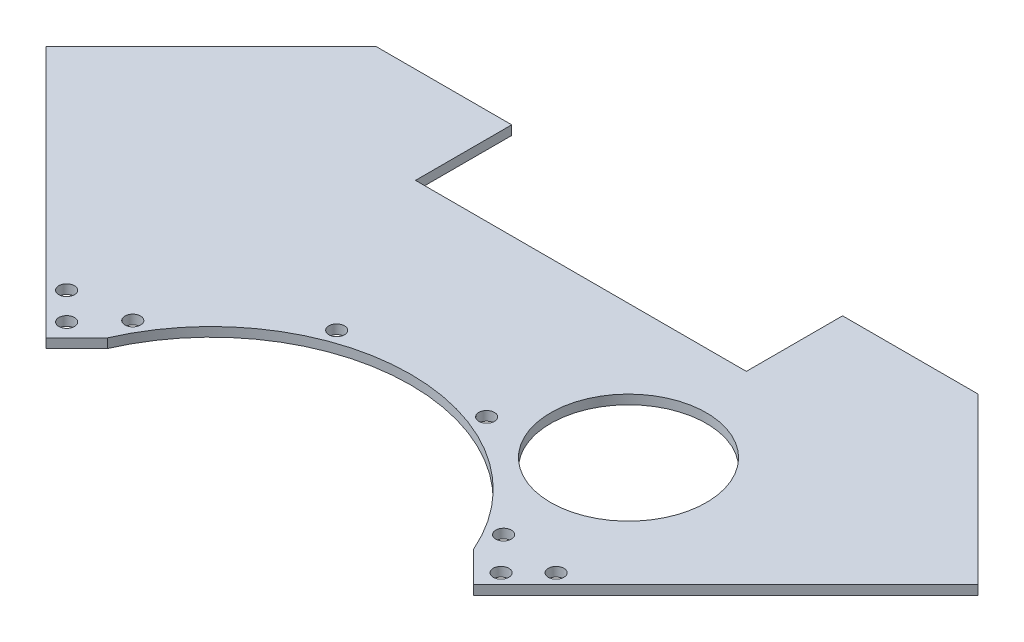
SolidWorks part; units mm, degrees
material "AISI Type A2 Tool Steel"
ref_plane "Front Plane" through (0, 0, 0) normal (0, 0, 1) x (1, 0, 0)
ref_plane "Top Plane" through (0, 0, 0) normal (0, 1, 0) x (1, 0, 0)
ref_plane "Right Plane" through (0, 0, 0) normal (1, 0, 0) x (0, 0, -1)
other "Bounding Box"
ref_plane "Default Plane" through (-8.9266, -12.7485, 0) normal (-0.1736, 0.9848, 0) x (0.9848, 0.1736, 0)
sketch "Sketch1" plane through (0, 0, 0) normal (0, 1, 0) x (1, 0, 0)
  line L0 (-78.7235, 24.8419) -> (78.7235, 24.8419) construction
  line L1 (0, 0) -> (139.7, 139.7) construction
  line L2 (0, 0) -> (-139.7, 139.7) construction
  line L3 (0, 0) -> (0, 165.1) construction
  line L4 (-139.7, 139.7) -> (139.7, 139.7) construction
  line L5 (-44.45, 203.2) -> (44.45, 203.2)
  line L6 (-44.45, 203.2) -> (-44.45, 127)
  line L7 (-44.45, 127) -> (44.45, 127)
  line L8 (44.45, 203.2) -> (44.45, 127)
  line L9 (-44.45, 203.2) -> (44.45, 127) construction
  line L10 (-44.45, 127) -> (44.45, 203.2) construction
  line L11 (-167.7633, 131.8423) -> (-131.8423, 167.7633)
  line L12 (-167.7633, 131.8423) -> (-147.5577, 111.6367)
  line L13 (-131.8423, 167.7633) -> (-111.6367, 147.5577)
  line L14 (-147.5577, 111.6367) -> (-111.6367, 147.5577)
  line L15 (-167.7633, 131.8423) -> (-111.6367, 147.5577) construction
  line L16 (-131.8423, 167.7633) -> (-147.5577, 111.6367) construction
  line L17 (131.8423, 167.7633) -> (167.7633, 131.8423)
  line L18 (131.8423, 167.7633) -> (111.6367, 147.5577)
  line L19 (167.7633, 131.8423) -> (147.5577, 111.6367)
  line L20 (111.6367, 147.5577) -> (147.5577, 111.6367)
  line L21 (131.8423, 167.7633) -> (147.5577, 111.6367) construction
  line L22 (167.7633, 131.8423) -> (111.6367, 147.5577) construction
  line L23 (-29.5981, 56.1801) -> (48.4616, 97.3054)
  line L24 (-9.525, -44.45) -> (9.525, -44.45)
  line L25 (-9.525, -44.45) -> (-9.525, 44.45)
  line L26 (-9.525, 44.45) -> (9.525, 44.45)
  line L27 (9.525, -44.45) -> (9.525, 44.45)
  line L28 (-9.525, -44.45) -> (9.525, 44.45) construction
  line L29 (-9.525, 44.45) -> (9.525, -44.45) construction
  line L30 (61.9263, -14.0491) -> (81.447, 71.9948)
  line L31 (78.7235, 24.8419) -> (194.7041, 140.8225)
  line L32 (-78.7235, 24.8419) -> (-194.7041, 140.8225)
  line L33 (-194.7041, 140.8225) -> (-138.6766, 196.85)
  line L34 (-138.6766, 196.85) -> (-53.975, 196.85)
  line L35 (-53.975, 196.85) -> (-53.975, 120.65)
  line L36 (-53.975, 120.65) -> (53.975, 120.65)
  line L37 (53.975, 120.65) -> (53.975, 196.85)
  line L38 (53.975, 196.85) -> (138.6766, 196.85)
  line L39 (138.6766, 196.85) -> (194.7041, 140.8225)
  line L40 (0, 0) -> (59.1288, 77.0581) construction
  circle A0 centre (0, 0) radius 63.5
  circle A1 centre (59.1288, 77.0581) radius 22.8854
  arc A2 (-78.7235, 24.8419) -> (78.7235, 24.8419) centre (0, 0) ccw
  circle A3 centre (59.1288, 77.0581) radius 29.5021
  point P4 (0, -82.55)
  point P39 (121.7395, 157.6605)
  point P44 (0, 63.5)
  dimension "D1" = 127
  dimension "D9" = 45.7708
  dimension "D12" = 19.05
  dimension "D20" = 59.0042
  dimension "D2" = 45
  dimension "D3" = 50.8
  dimension "D4" = 28.575
  dimension "D5" = 88.9
  dimension "D6" = 19.05
  dimension "D7" = 76.2
  dimension "D8" = 88.9
  dimension "D10" = 25.4
  dimension "D11" = 139.7
  dimension "D13" = 9.525
  dimension "D14" = 6.35
  dimension "D15" = 38.1
  dimension "D16" = 31.75
  dimension "D17" = 25.4
  dimension "D18" = 97.1296
  dimension "D19" = 37.5
sketch "Sketch2" plane through (0, 0, 0) normal (1, 0, 0) x (0, 0, -1)
  line L0 (-82.55, -25.4) -> (-82.55, 25.4)
  line L1 (-63.5, 17.78) -> (63.5, 17.78)
  line L2 (-63.5, 17.78) -> (-63.5, -17.78)
  line L3 (-63.5, -17.78) -> (63.5, -17.78)
  line L4 (63.5, 17.78) -> (63.5, -17.78)
  line L5 (-63.5, 17.78) -> (63.5, -17.78) construction
  line L6 (-63.5, -17.78) -> (63.5, 17.78) construction
  line L7 (-82.55, 25.4) -> (82.55, 25.4)
  line L8 (-82.55, -25.4) -> (63.5, -25.4)
  line L9 (63.5, -25.4) -> (63.5, -38.1)
  line L10 (0, -44.45) -> (25.3029, -44.45) construction
  line L11 (139.7, -44.45) -> (139.7, 6.35) construction
  line L12 (63.5, -38.1) -> (194.5388, -38.1)
  line L13 (165.1, 0) -> (165.1, -3.81) construction
  line L14 (203.2, -3.81) -> (203.2, 0) construction
  line L15 (165.1, -41.91) -> (165.1, -44.45) construction
  line L16 (157.6605, -19.05) -> (157.6605, 0) construction
  line L17 (196.85, -44.45) -> (181.8826, -3.3274)
  line L18 (181.8826, -3.3274) -> (82.55, -3.3274)
  line L19 (82.55, -3.3274) -> (82.55, 25.4)
  line L20 (63.5, -38.1) -> (63.5, -41.1226)
  line L21 (63.5, -41.1226) -> (195.6389, -41.1226)
  line L22 (82.55, -3.3274) -> (82.55, -6.35)
  line L23 (82.55, -6.35) -> (182.9827, -6.35)
  circle A0 centre (0, 0) radius 44.45
  circle A1 centre (165.1, -3.81) radius 38.1
  circle A2 centre (165.1, -3.81) radius 6.35
  ellipse E0 centre (139.7, -19.05) end of major axis (139.7, 6.35) minor radius 17.9605
  dimension "D4" = 12.7
  dimension "D1" = 35.56
  dimension "D2" = 50.8
  dimension "D3" = 50.8
  dimension "D5" = 34.29
  dimension "D6" = 12.7
  dimension "D7" = 70
  dimension "D8" = 3.0226
  dimension "D9" = 31.75
  dimension "D10" = 19.05
ref_plane "Plane1" through (-129.5972, 0, -129.5972) normal (-0.7071, 0, -0.7071) x (0.7071, 0, -0.7071)
sketch "Sketch5" plane through (-129.5972, 0, -129.5972) normal (-0.7071, 0, -0.7071) x (0.7071, 0, -0.7071)
  line L0 (-141421.3562, 44.45) -> (141439.2481, 44.45) construction
  line L1 (0, 19.05) -> (0, 0) construction
  circle A0 centre (0, 19.05) radius 25.4
  dimension "D1" = 50.8
sketch "Sketch3" plane through (0, 0, 0) normal (0, 1, 0) x (1, 0, 0)
  line L0 (64.2555, 10.3739) -> (152.0479, 98.1663)
  line L1 (78.7235, 24.8419) -> (194.7041, 140.8225) construction
  line L2 (152.0479, 98.1663) -> (98.1663, 152.0479)
  line L3 (98.1663, 152.0479) -> (53.975, 152.0479)
  line L4 (53.975, 120.65) -> (53.975, 196.85) construction
  line L5 (53.975, 152.0479) -> (53.975, 120.65)
  line L6 (53.975, 120.65) -> (-53.975, 120.65)
  line L7 (-53.975, 120.65) -> (-53.975, 152.0479)
  line L8 (-53.975, 196.85) -> (-53.975, 120.65) construction
  line L9 (-53.975, 152.0479) -> (-98.1663, 152.0479)
  line L10 (-98.1663, 152.0479) -> (-152.0479, 98.1663)
  line L11 (-78.7235, 24.8419) -> (-194.7041, 140.8225) construction
  line L12 (-152.0479, 98.1663) -> (-64.2555, 10.3739)
  line L13 (-147.5577, 111.6367) -> (-111.6367, 147.5577) construction
  line L14 (111.6367, 147.5577) -> (147.5577, 111.6367) construction
  line L15 (0, 0) -> (-139.7, 139.7) construction
  arc A0 (-64.2555, 10.3739) -> (64.2555, 10.3739) centre (0, 0) cw
  circle A2 centre (0, 0) radius 63.5 construction
  point P34 (-125.1071, 125.1071)
  dimension "D1" = 1.5875
  dimension "D2" = 6.35
extrude "Boss-Extrude1" add sketch "Sketch3" along normal mid plane 3.0226
sketch "Sketch4" plane through (0, 1.5113, 0) normal (0, 1, 0) x (1, 0, 0)
  line L1 (0, 0) -> (24.462, 65.4266) construction
  line L2 (0, 0) -> (60.4919, 34.925) construction
  line L3 (0, 0) -> (23.1311, 0) construction
  line L4 (0, 0) -> (0, 21.8416) construction
  circle A0 centre (24.462, 65.4266) radius 2.5527
  circle A1 centre (24.462, 65.4266) radius 4.7625 construction
  arc A2 (64.2555, 10.3739) -> (-64.2555, 10.3739) centre (0, 0) ccw construction
  circle A3 centre (60.4919, 34.925) radius 2.5527
  circle A4 centre (60.4919, 34.925) radius 4.7625 construction
  circle A5 centre (-60.4919, 34.925) radius 2.5527
  circle A6 centre (-24.462, 65.4266) radius 2.5527
  dimension "D1" = 5.1054
  dimension "D2" = 9.525
  dimension "D3" = 20.5
  dimension "D4" = 30
extrude "Cut-Extrude1" cut sketch "Sketch4" against normal through all
sketch "Sketch6" plane through (0, 1.5113, 0) normal (0, 1, 0) x (1, 0, 0)
  line L0 (78.7235, 24.8419) -> (69.7432, 15.8617) construction
  line L1 (64.2555, 10.3739) -> (152.0479, 98.1663) construction
  line L2 (69.7432, 15.8617) -> (60.7629, 24.8419)
  line L3 (60.7629, 24.8419) -> (73.5003, 37.5793) construction
  line L4 (78.7235, 24.8419) -> (73.5003, 37.5793) construction
  line L5 (60.7629, 24.8419) -> (59.7182, 25.8866)
  line L6 (59.7182, 25.8866) -> (64.2555, 10.3739)
  line L7 (64.2555, 10.3739) -> (69.7432, 15.8617)
  circle A0 centre (0, 0) radius 82.55 construction
  arc A1 (64.2555, 10.3739) -> (-64.2555, 10.3739) centre (0, 0) ccw construction
  dimension "D1" = 165.1
  dimension "D2" = 12.7
  dimension "D3" = 12.7
extrude "Cut-Extrude4" cut sketch "Sketch6" against normal through all
sketch "Sketch7" plane through (0, 1.5113, 0) normal (0, 1, 0) x (1, 0, 0)
  line L0 (66.3756, 19.2293) -> (70.8657, 23.7194) construction
  line L2 (70.8657, 23.7194) -> (79.846, 32.6996) construction
  line L3 (69.7432, 15.8617) -> (59.7182, 25.8866) construction
  line L4 (78.7235, 24.8419) -> (194.7041, 140.8225) construction
  circle A0 centre (70.8657, 23.7194) radius 2.5527
  circle A1 centre (79.846, 32.6996) radius 2.5527
  dimension "D1" = 5.1054
  dimension "D2" = 6.35
  dimension "D3" = 12.7
  dimension "D4" = 4.7625
extrude "Cut-Extrude2" cut sketch "Sketch7" against normal through all
sketch "Sketch22" [suppressed] plane through (0, 1.5113, 0) normal (0, 1, 0) x (1, 0, 0)
  circle A0 centre (59.1288, 77.0581) radius 31.75
  dimension "D1" = 63.5
extrude "Cut-Extrude5" [suppressed] cut sketch "Sketch22" against normal through all
mirror "Mirror1" about plane through (0, 0, 0) normal (1, 0, 0) of "Cut-Extrude4", "Cut-Extrude2"
sketch "Sketch8" plane through (0, 1.5113, 0) normal (0, 1, 0) x (1, 0, 0)
  circle A0 centre (59.1288, 77.0581) radius 25.4
  dimension "D1" = 50.8
extrude "Cut-Extrude3" cut sketch "Sketch8" against normal through all
ref_plane "Plane2" [suppressed] through (26.9408, 0, 26.9408) normal (-0.7071, 0, -0.7071) x (0.7071, 0, -0.7071)
sketch "Sketch10" [suppressed] plane through (26.9408, 0, 26.9408) normal (-0.7071, 0, -0.7071) x (0.7071, 0, -0.7071)
  line L0 (-141421.3562, 44.45) -> (141439.2481, 44.45) construction
  line L1 (-141421.3562, 44.45) -> (141439.2481, 44.45) construction
  line L2 (44.9013, 41.1226) -> (237.2531, 41.1226)
  line L3 (237.2531, 41.1226) -> (223.4968, 3.3274)
  line L4 (223.4968, 3.3274) -> (58.3717, 3.3274)
  line L5 (237.2531, 41.1226) -> (238.4642, 44.45)
  dimension "D1" = 70
ref_plane "Plane5" [suppressed] through (0, -44.45, 0) normal (0, 1, 0) x (1, 0, 0)
ref_plane "Plane6" [suppressed] through (0, -3.3274, 0) normal (0, 1, 0) x (1, 0, 0)
sketch "Sketch20" [suppressed] plane through (0, -3.3274, 0) normal (0, 1, 0) x (1, 0, 0)
  line L0 (184.9769, 131.0953) -> (134.1896, 181.8826)
  line L1 (134.1896, 181.8826) -> (53.975, 181.8826)
  line L2 (138.6766, 196.85) -> (194.7041, 140.8225) construction
  line L3 (53.975, 120.65) -> (53.975, 196.85) construction
  line L4 (184.9769, 131.0953) -> (186.5933, 132.7118) construction
  line L5 (186.5933, 132.7118) -> (135.1365, 184.1686)
  line L6 (135.1365, 184.1686) -> (53.975, 184.1686)
  line L7 (53.975, 184.1686) -> (53.975, 181.8826)
  line L8 (184.9769, 131.0953) -> (187.1142, 128.958)
  line L9 (187.1142, 128.958) -> (188.7306, 130.5745)
  line L10 (188.7306, 130.5745) -> (186.5933, 132.7118)
  dimension "D1" = 2.286
  dimension "D2" = 3.0226
sketch "Sketch21" [suppressed] plane through (0, -44.45, 0) normal (0, 1, 0) x (1, 0, 0)
  line L0 (195.5604, 141.6789) -> (140.3893, 196.85)
  line L1 (140.3893, 196.85) -> (53.975, 196.85)
  line L2 (195.5604, 141.6789) -> (197.6977, 139.5416)
  line L3 (138.6766, 196.85) -> (194.7041, 140.8225) construction
  line L4 (195.5604, 141.6789) -> (197.1769, 143.2953) construction
  line L5 (197.1769, 143.2953) -> (141.3362, 199.136)
  line L6 (141.3362, 199.136) -> (53.975, 199.136)
  line L7 (53.975, 199.136) -> (53.975, 196.85)
  line L8 (197.6977, 139.5416) -> (199.3142, 141.158)
  line L9 (199.3142, 141.158) -> (197.1769, 143.2953)
  dimension "D1" = 2.286
  dimension "D2" = 3.0226
loft "Loft1" [suppressed] add profiles "Sketch20", "Sketch21"
fillet "Fillet1" [suppressed] radius 12.7
mirror "Mirror4" [suppressed] about plane through (0, 0, 0) normal (1, 0, 0)
